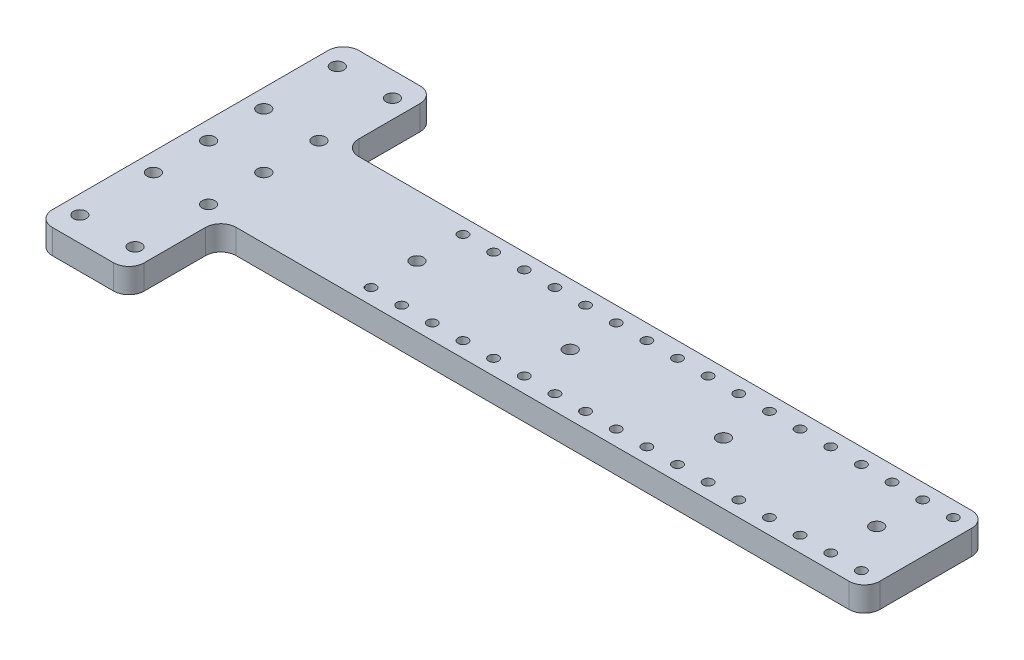
SolidWorks part; units mm, degrees
ref_plane "Front Plane" through (0, 0, 0) normal (0, 0, 1) x (1, 0, 0)
ref_plane "Top Plane" through (0, 0, 0) normal (0, 1, 0) x (1, 0, 0)
ref_plane "Right Plane" through (0, 0, 0) normal (1, 0, 0) x (0, 0, -1)
sketch "Sketch1" plane through (0, 0, 0) normal (0, 1, 0) x (1, 0, 0)
  line L1 (-15, 50) -> (15, 50)
  line L2 (-15, 50) -> (-15, -50)
  line L3 (-15, -50) -> (15, -50)
  line L4 (15, 50) -> (15, -50)
  line L5 (-15, 50) -> (15, -50) construction
  line L6 (-15, -50) -> (15, 50) construction
  line L7 (15, 20) -> (225, 20)
  line L8 (15, 20) -> (15, -20)
  line L9 (15, -20) -> (225, -20)
  line L10 (225, 20) -> (225, -20)
  line L11 (120, -20) -> (120, 20) construction
  line L12 (15, 0) -> (225, 0) construction
  point P0 (0, 0)
  point P338 (120, 0)
  dimension "D1" = 30
  dimension "D2" = 100
  dimension "D3" = 40
  dimension "D4" = 210
extrude "Boss-Extrude1" add sketch "Sketch1" along normal blind 8 contours L4 L1 L2 L3 | L10 L7 L4 L9
sketch "Sketch2" plane through (0, 8, 0) normal (0, 1, 0) x (1, 0, 0)
  line L0 (-9, 0) -> (9, 0) construction
  line L1 (-9, -30) -> (9, -30) construction
  line L2 (-9, -30) -> (-9, 30) construction
  line L3 (-9, 30) -> (9, 30) construction
  line L4 (9, -30) -> (9, 30) construction
  line L5 (-9, -30) -> (9, 30) construction
  line L6 (-9, 30) -> (9, -30) construction
  line L7 (9, -42) -> (-9, -42) construction
  line L8 (9, -42) -> (9, -18) construction
  line L9 (9, -18) -> (-9, -18) construction
  line L10 (-9, -42) -> (-9, -18) construction
  line L11 (9, -42) -> (-9, -18) construction
  line L12 (9, -18) -> (-9, -42) construction
  circle A0 centre (-9, -42) radius 2.1
  circle A1 centre (-9, -18) radius 2.1
  circle A2 centre (9, -18) radius 2.1
  circle A3 centre (9, -42) radius 2.1
  circle A4 centre (9, 42) radius 2.1
  circle A5 centre (9, 18) radius 2.1
  circle A6 centre (-9, 18) radius 2.1
  circle A7 centre (-9, 42) radius 2.1
  point P0 (0, 0)
  point P6 (0, -30)
  dimension "D4" = 4.2
  dimension "D1" = 18
  dimension "D2" = 60
  dimension "D3" = 24
sketch "Sketch3" plane through (0, 8, 0) normal (0, 1, 0) x (1, 0, 0)
  line L0 (-9, 0) -> (9, 0) construction
  circle A0 centre (-9, 0) radius 2.1
  circle A1 centre (9, 0) radius 2.1
  circle A2 centre (59, 0) radius 2.1
  circle A3 centre (109, 0) radius 2.1
  circle A4 centre (159, 0) radius 2.1
  circle A5 centre (209, 0) radius 2.1
  point P4 (0, 0)
  point P8 (50, 0)
  point P11 (100, 0)
  point P14 (150, 0)
  point P17 (200, 0)
  dimension "D2" = 4.2
  dimension "D1" = 18
  dimension "D4" = 50
  dimension "D3" = 5
extrude "Cut-Extrude2" cut sketch "Sketch3" against normal blind 10
extrude "Cut-Extrude3" cut sketch "Sketch2" against normal blind 10
sketch "Sketch4" plane through (0, 8, 0) normal (0, 1, 0) x (1, 0, 0)
  line L0 (59, 0) -> (59, -15) construction
  line L1 (59, 0) -> (109, 0) construction
  circle A0 centre (59, -15) radius 1.6
  circle A1 centre (59, 15) radius 1.6
  circle A2 centre (69, 15) radius 1.6
  circle A3 centre (69, -15) radius 1.6
  circle A4 centre (79, 15) radius 1.6
  circle A5 centre (79, -15) radius 1.6
  circle A6 centre (89, 15) radius 1.6
  circle A7 centre (89, -15) radius 1.6
  circle A8 centre (99, -15) radius 1.6
  circle A9 centre (99, 15) radius 1.6
  circle A10 centre (109, -15) radius 1.6
  circle A11 centre (109, 15) radius 1.6
  circle A12 centre (119, -15) radius 1.6
  circle A13 centre (119, 15) radius 1.6
  circle A14 centre (129, -15) radius 1.6
  circle A15 centre (129, 15) radius 1.6
  circle A16 centre (139, -15) radius 1.6
  circle A17 centre (139, 15) radius 1.6
  circle A18 centre (149, -15) radius 1.6
  circle A19 centre (149, 15) radius 1.6
  circle A20 centre (159, -15) radius 1.6
  circle A21 centre (159, 15) radius 1.6
  circle A22 centre (169, -15) radius 1.6
  circle A23 centre (169, 15) radius 1.6
  circle A24 centre (179, -15) radius 1.6
  circle A25 centre (179, 15) radius 1.6
  circle A26 centre (189, 15) radius 1.6
  circle A27 centre (189, -15) radius 1.6
  circle A28 centre (199, 15) radius 1.6
  circle A29 centre (199, -15) radius 1.6
  circle A30 centre (209, 15) radius 1.6
  circle A31 centre (209, -15) radius 1.6
  circle A32 centre (219, 15) radius 1.6
  circle A33 centre (219, -15) radius 1.6
  dimension "D2" = 3.2
  dimension "D1" = 15
  dimension "D4" = 10
  dimension "D6" = 10
  dimension "D8" = 10
  dimension "D3" = 4
  dimension "D5" = 10
  dimension "D7" = 5
extrude "Cut-Extrude4" cut sketch "Sketch4" against normal blind 10
fillet "Fillet1" radius 5 8 edges at (-15, 4, 50) (15, 4, -20) (15, 4, -50) (-15, 4, -50) (225, 4, -20) (225, 4, 20) (15, 4, 20) (15, 4, 50)
